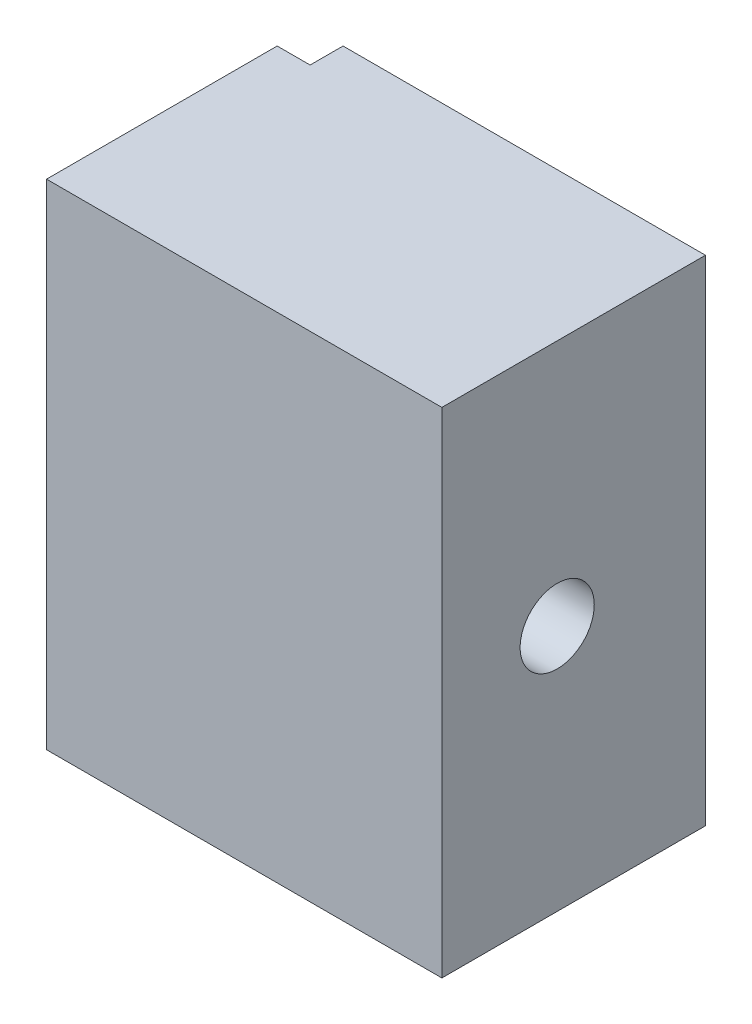
SolidWorks part; units mm, degrees
material "Plain Carbon Steel"
ref_plane "Front Plane" through (0, 0, 0) normal (0, 0, 1) x (1, 0, 0)
ref_plane "Top Plane" through (0, 0, 0) normal (0, 1, 0) x (1, 0, 0)
ref_plane "Right Plane" through (0, 0, 0) normal (1, 0, 0) x (0, 0, -1)
sketch "Sketch1" plane through (0, 0, 0) normal (1, 0, 0) x (0, 0, -1)
  line L1 (0, 0) -> (-16, 0)
  line L2 (0, 0) -> (0, 30)
  line L3 (0, 30) -> (-16, 30)
  line L4 (-16, 0) -> (-16, 30)
  dimension "D1" = 30
  dimension "D2" = 16
extrude "Boss-Extrude1" add sketch "Sketch1" along normal blind 24
sketch "Sketch2" plane through (0, 0, 0) normal (-1, 0, 0) x (0, 0, 1)
  line L0 (16, 0) -> (0, 0) construction
  line L1 (0, 30) -> (2, 30)
  line L2 (0, 30) -> (0, 0)
  line L3 (0, 0) -> (2, 0)
  line L4 (2, 30) -> (2, 0)
  dimension "D1" = 2
extrude "Cut-Extrude1" cut sketch "Sketch2" against normal blind 2
hole_wizard "M4 Clearance Hole1" positions "Sketch4" profile "Sketch5" hole size "M4" standard "ISO" end condition through all
sketch "Sketch4" plane through (24, 0, 0) normal (1, 0, 0) x (0, 0, -1)
  line L0 (0, 30) -> (-16, 30) construction
  line L1 (-16, 30) -> (-16, 0) construction
  point P0 (-9, 15)
  dimension "D1" = 15
  dimension "D2" = 7
sketch "Sketch5" plane through (24, 15, 9) normal (0, 1, 0) x (0, 0, -1)
  line L0 (0, 0) -> (0, 24)
  line L1 (0, 24) -> (2.25, 24)
  line L2 (2.25, 24) -> (2.25, 0)
  line L5 (2.25, 0) -> (0, 0)
  line L11 (0, -6.35) -> (0, 107.95) construction
  dimension "Thru Hole Dia." = 4.5
  dimension "Thru Hole Depth" = 24
